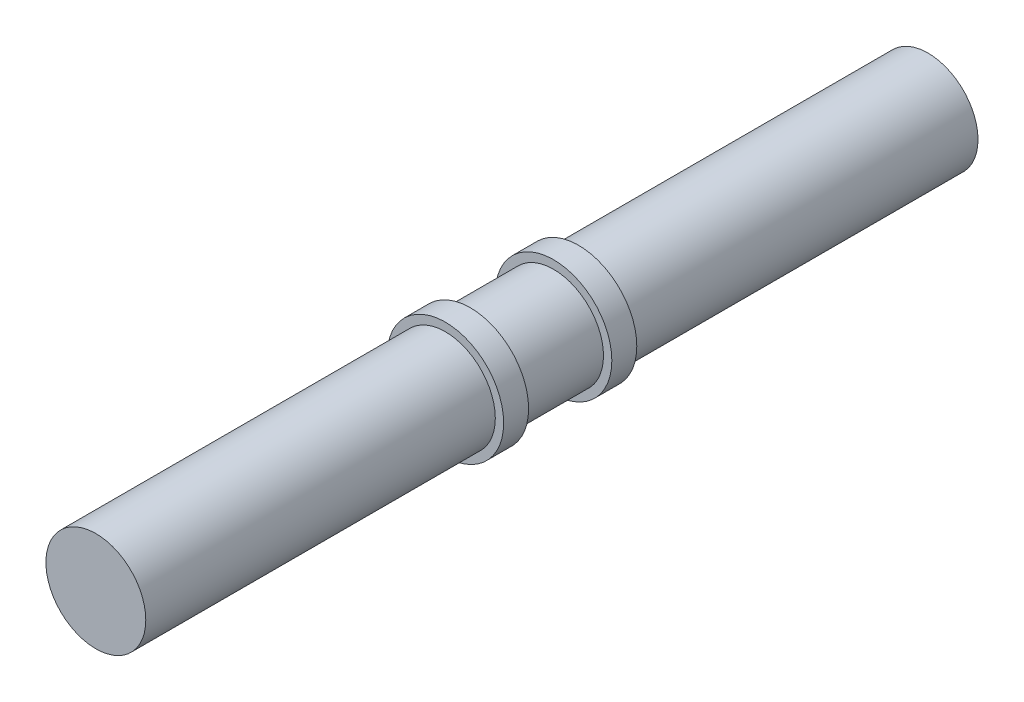
SolidWorks part; units mm, degrees
ref_plane "Front Plane" through (0, 0, 0) normal (0, 0, 1) x (1, 0, 0)
ref_plane "Top Plane" through (0, 0, 0) normal (0, 1, 0) x (1, 0, 0)
ref_plane "Right Plane" through (0, 0, 0) normal (1, 0, 0) x (0, 0, -1)
sketch "Sketch1" plane through (0, 0, 0) normal (0, 0, 1) x (1, 0, 0)
  circle A0 centre (0, 0) radius 6
  dimension "D1" = 12
extrude "Boss-Extrude1" add sketch "Sketch1" along normal blind 42 contours A0
sketch "Sketch2" plane through (0, 0, 42) normal (0, 0, 1) x (1, 0, 0)
  circle A0 centre (0, 0) radius 7
extrude "Boss-Extrude2" add sketch "Sketch2" along normal blind 3
sketch "Sketch3" plane through (0, 0, 45) normal (0, 0, 1) x (1, 0, 0)
  circle A0 centre (0, 0) radius 6
extrude "Boss-Extrude3" add sketch "Sketch3" along normal blind 10
sketch "Sketch4" plane through (0, 0, 55) normal (0, 0, 1) x (1, 0, 0)
  circle A0 centre (0, 0) radius 7
extrude "Boss-Extrude4" add sketch "Sketch4" along normal blind 3
sketch "Sketch5" plane through (0, 0, 58) normal (0, 0, 1) x (1, 0, 0)
  circle A0 centre (0, 0) radius 6
extrude "Boss-Extrude5" add sketch "Sketch5" along normal blind 42
